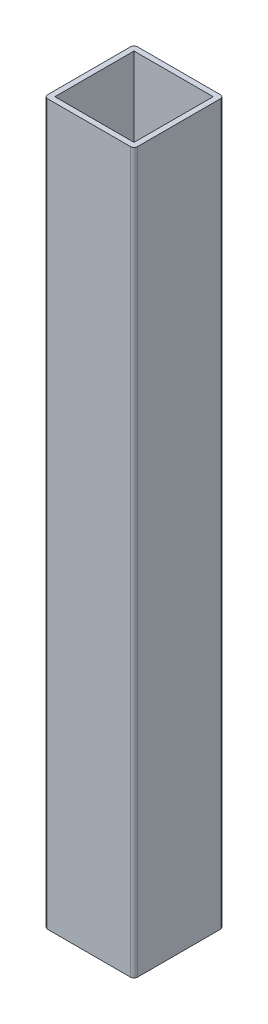
SolidWorks part; units mm, degrees
ref_plane "Front Plane" through (0, 0, 0) normal (0, 0, 1) x (1, 0, 0)
ref_plane "Top Plane" through (0, 0, 0) normal (0, 1, 0) x (1, 0, 0)
ref_plane "Right Plane" through (0, 0, 0) normal (1, 0, 0) x (0, 0, -1)
sketch "Sketch1" plane through (0, 0, 0) normal (0, 1, 0) x (1, 0, 0)
  line L0 (3, 47) -> (47, 47)
  line L1 (2, 0) -> (48, 0)
  line L2 (0, 2) -> (0, 48)
  line L3 (2, 50) -> (48, 50)
  line L4 (50, 2) -> (50, 48)
  line L5 (47, 3) -> (47, 47)
  line L6 (3, 3) -> (47, 3)
  line L7 (3, 3) -> (3, 47)
  arc A0 (2, 0) -> (0, 2) centre (2, 2) cw
  arc A1 (48, 0) -> (50, 2) centre (48, 2) ccw
  arc A2 (48, 50) -> (50, 48) centre (48, 48) cw
  arc A3 (0, 48) -> (2, 50) centre (2, 48) cw
  arc A4 (47, 47) -> (47, 47) centre (47, 47) cw
  arc A5 (47, 3) -> (47, 3) centre (47, 3) ccw
  arc A6 (3, 3) -> (3, 3) centre (3, 3) cw
  arc A7 (3, 47) -> (3, 47) centre (3, 47) cw
  point P7 (0, 0)
  point P14 (0, 50)
  dimension "D2" = 2
  dimension "D1" = 50
  dimension "D3" = 3
extrude "Boss-Extrude1" add sketch "Sketch1" along normal blind 400
